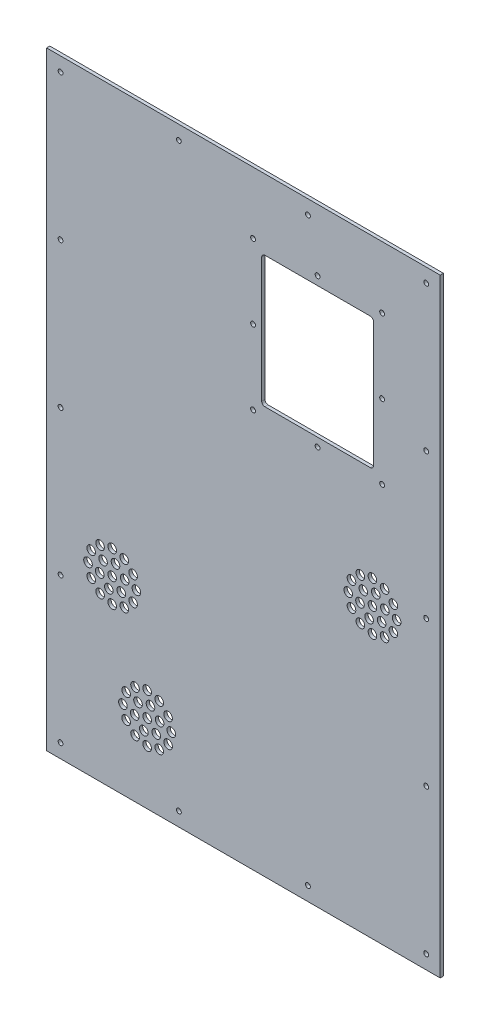
SolidWorks part; units mm, degrees
ref_plane "Спереди" through (0, 0, 0) normal (0, 0, 1) x (1, 0, 0)
ref_plane "Сверху" through (0, 0, 0) normal (0, 1, 0) x (1, 0, 0)
ref_plane "Справа" through (0, 0, 0) normal (1, 0, 0) x (0, 0, -1)
sketch "Эскиз1" plane through (0, 0, 0) normal (0, 0, 1) x (1, 0, 0)
  line L0 (0, 0) -> (366, 0)
  line L1 (0, 0) -> (0, 566)
  line L2 (366, 0) -> (366, 566)
  line L3 (0, 566) -> (366, 566)
  dimension "D1" = 566
  dimension "D2" = 366
extrude "Бобышка-Вытянуть1" add sketch "Эскиз1" along normal blind 3
sketch "Эскиз2" plane through (0, 0, 3) normal (0, 0, 1) x (1, 0, 0)
  line L0 (3, 563) -> (363, 563) construction
  line L1 (3, 563) -> (3, 3) construction
  line L2 (363, 563) -> (363, 3) construction
  line L3 (3, 3) -> (363, 3) construction
  line L4 (0, 566) -> (0, 0) construction
  line L5 (0, 0) -> (366, 0) construction
  dimension "D1" = 560
  dimension "D2" = 360
  dimension "D3" = 3
  dimension "D4" = 3
sketch "Эскиз5" plane through (0, 0, 0) normal (0, 0, -1) x (-1, 0, 0)
  line L0 (-353, 553) -> (-13, 553) construction
  line L1 (-353, 553) -> (-353, 13) construction
  line L2 (-13, 553) -> (-13, 13) construction
  line L3 (-353, 13) -> (-13, 13) construction
  line L4 (-366, 566) -> (0, 566) construction
  line L5 (-366, 0) -> (-366, 566) construction
  line L6 (0, 566) -> (0, 0) construction
  line L7 (0, 0) -> (-366, 0) construction
  line L8 (-366, 23) -> (-343, 23) construction
  line L9 (-366, 23) -> (-366, 0) construction
  line L10 (-343, 23) -> (-343, 0) construction
  line L11 (-366, 0) -> (-343, 0) construction
  line L12 (0, 0) -> (0, 23) construction
  line L13 (0, 0) -> (-23, 0) construction
  line L14 (0, 23) -> (-23, 23) construction
  line L15 (-23, 0) -> (-23, 23) construction
  line L16 (-366, 566) -> (-343, 566) construction
  line L17 (-366, 566) -> (-366, 543) construction
  line L18 (-343, 566) -> (-343, 543) construction
  line L19 (-366, 543) -> (-343, 543) construction
  line L20 (0, 566) -> (0, 543) construction
  line L21 (0, 566) -> (-23, 566) construction
  line L22 (0, 543) -> (-23, 543) construction
  line L23 (-23, 566) -> (-23, 543) construction
  line L24 (-13, 283) -> (-353, 283) construction
  line L25 (-183, 553) -> (-183, 13) construction
  circle A0 centre (-353, 553) radius 2.25
  circle A1 centre (-13, 553) radius 2.25
  circle A3 centre (-243, 553) radius 2.25
  circle A4 centre (-123, 553) radius 2.25
  circle A5 centre (-353, 418) radius 2.25
  circle A6 centre (-353, 283) radius 2.25
  circle A7 centre (-353, 148) radius 2.25
  circle A8 centre (-353, 13) radius 2.25
  circle A11 centre (-13, 418) radius 2.25
  circle A12 centre (-13, 283) radius 2.25
  circle A13 centre (-13, 148) radius 2.25
  circle A14 centre (-13, 13) radius 2.25
  circle A18 centre (-123, 13) radius 2.25
  circle A19 centre (-243, 13) radius 2.25
  dimension "D13" = 4.5
  dimension "D14" = 4.5
  dimension "D15" = 110
  dimension "D17" = 4.5
  dimension "D18" = 4.5
  dimension "D19" = 110
  dimension "D22" = 135
  dimension "D23" = 135
  dimension "D24" = 110
  dimension "D25" = 5
  dimension "D26" = 135
  dimension "D27" = 110
  dimension "D29" = 4.5
  dimension "D31" = 4.5
  dimension "D1" = 13
  dimension "D2" = 13
  dimension "D3" = 13
  dimension "D4" = 13
  dimension "D5" = 23
  dimension "D6" = 23
  dimension "D7" = 23
  dimension "D8" = 23
  dimension "D9" = 23
  dimension "D10" = 23
  dimension "D11" = 23
  dimension "D12" = 23
  dimension "D21" = 5
extrude "Вырез-Вытянуть2" cut sketch "Эскиз5" against normal through all
sketch "Эскиз6" plane through (0, 0, 3) normal (0, 0, 1) x (1, 0, 0)
  line L0 (200, 378.5) -> (200, 500.5) construction
  line L1 (200, 378.5) -> (200, 500.5)
  line L2 (200, 500.5) -> (304, 500.5) construction
  line L3 (200, 500.5) -> (304, 500.5)
  line L4 (304, 500.5) -> (304, 378.5) construction
  line L5 (304, 500.5) -> (304, 378.5)
  line L6 (304, 378.5) -> (200, 378.5) construction
  line L7 (304, 378.5) -> (200, 378.5)
extrude "Вырез-Вытянуть3" cut sketch "Эскиз6" against normal through all
sketch "Эскиз7" plane through (0, 0, 3) normal (0, 0, 1) x (1, 0, 0)
  circle A0 centre (192, 370.5) radius 2.25 construction
  circle A1 centre (192, 370.5) radius 2.25
  circle A2 centre (192, 439.5) radius 2.25 construction
  circle A3 centre (192, 439.5) radius 2.25
  circle A4 centre (192, 508.5) radius 2.25 construction
  circle A5 centre (192, 508.5) radius 2.25
  circle A6 centre (252, 370.5) radius 2.25 construction
  circle A7 centre (252, 370.5) radius 2.25
  circle A8 centre (312, 370.5) radius 2.25 construction
  circle A9 centre (312, 370.5) radius 2.25
  circle A10 centre (252, 508.5) radius 2.25 construction
  circle A11 centre (252, 508.5) radius 2.25
  circle A12 centre (312, 508.5) radius 2.25 construction
  circle A13 centre (312, 508.5) radius 2.25
  circle A14 centre (312, 439.5) radius 2.25 construction
  circle A15 centre (312, 439.5) radius 2.25
  circle A16 centre (312, 370.5) radius 2.25
extrude "Вырез-Вытянуть4" cut sketch "Эскиз7" against normal through all contours A3 | A11 | A13 | A15 | A9 | A7 | A1 | A5
fillet "Fillet2" radius 3 4 edges at (200, 378.5, 1.5) (304, 378.5, 1.5) (304, 500.5, 1.5) (200, 500.5, 1.5)
sketch "Эскиз8" plane through (0, 0, 0) normal (0, 0, -1) x (-1, 0, 0)
  line L0 (-93.5, 73) -> (-93.5, 0) construction
  line L1 (0, 0) -> (-366, 0) construction
  line L2 (-61, 171) -> (0, 171) construction
  line L3 (0, 566) -> (0, 0) construction
  line L4 (-93.5, 73) -> (0, 73) construction
  line L5 (-61, 171) -> (-76.9099, 155.0901) construction
  line L6 (-93.5, 73) -> (-101.9853, 64.5147) construction
  line L7 (-61, 193.5) -> (-61, 148.5) construction
  circle A0 centre (-61, 171) radius 12 construction
  circle A1 centre (-61, 171) radius 22.5 construction
  circle A2 centre (-61, 148.5) radius 4
  circle A3 centre (-69.4853, 162.5147) radius 4
  circle A4 centre (-61, 171) radius 4
  circle A5 centre (-72.25, 151.5144) radius 4
  circle A6 centre (-80.4856, 159.75) radius 4
  circle A7 centre (-83.5, 171) radius 4
  circle A8 centre (-80.4856, 182.25) radius 4
  circle A9 centre (-72.25, 190.4856) radius 4
  circle A10 centre (-61, 193.5) radius 4
  circle A11 centre (-49.75, 190.4856) radius 4
  circle A12 centre (-41.5144, 182.25) radius 4
  circle A13 centre (-38.5, 171) radius 4
  circle A14 centre (-41.5144, 159.75) radius 4
  circle A15 centre (-49.75, 151.5144) radius 4
  circle A16 centre (-72.5911, 174.1058) radius 4
  circle A17 centre (-64.1058, 182.5911) radius 4
  circle A18 centre (-52.5147, 179.4853) radius 4
  circle A19 centre (-49.4089, 167.8942) radius 4
  circle A20 centre (-57.8942, 159.4089) radius 4
  circle A21 centre (-93.5, 73) radius 12 construction
  circle A22 centre (-93.5, 73) radius 22.5 construction
  circle A23 centre (-93.5, 73) radius 4
  circle A24 centre (-93.5, 50.5) radius 4
  circle A25 centre (-101.9853, 64.5147) radius 4
  circle A26 centre (-104.75, 53.5144) radius 4
  circle A27 centre (-112.9856, 61.75) radius 4
  circle A28 centre (-116, 73) radius 4
  circle A29 centre (-112.9856, 84.25) radius 4
  circle A30 centre (-104.75, 92.4856) radius 4
  circle A31 centre (-93.5, 95.5) radius 4
  circle A32 centre (-82.25, 92.4856) radius 4
  circle A33 centre (-74.0144, 84.25) radius 4
  circle A34 centre (-71, 73) radius 4
  circle A35 centre (-74.0144, 61.75) radius 4
  circle A36 centre (-82.25, 53.5144) radius 4
  circle A37 centre (-105.0911, 76.1058) radius 4
  circle A38 centre (-96.6058, 84.5911) radius 4
  circle A39 centre (-85.0147, 81.4853) radius 4
  circle A40 centre (-81.9089, 69.8942) radius 4
  circle A41 centre (-90.3942, 61.4089) radius 4
  point P26 (-61, 171)
  point P52 (-61, 171)
  point P82 (-93.5, 73)
  point P93 (-93.5, 73)
  dimension "D4" = 45
  dimension "D5" = 24
  dimension "D7" = 8
  dimension "D8" = 8
  dimension "D9" = 8
  dimension "D12" = 8
  dimension "D13" = 8
  dimension "D14" = 8
  dimension "D16" = 24
  dimension "D17" = 45
  dimension "D1" = 73
  dimension "D2" = 61
  dimension "D3" = 93.5
  dimension "D6" = 45
  dimension "D15" = 171
  dimension "D20" = 45
  dimension "D10" = 12
  dimension "D11" = 6
  dimension "D18" = 12
  dimension "D19" = 6
extrude "Вырез-Вытянуть5" cut sketch "Эскиз8" against normal through all
sketch "Эскиз9" plane through (0, 0, 0) normal (0, 0, -1) x (-1, 0, 0)
  line L0 (-303, 566) -> (-303, 268) construction
  line L1 (-366, 566) -> (0, 566) construction
  line L2 (-303, 268) -> (-366, 268) construction
  line L3 (-366, 0) -> (-366, 566) construction
  line L4 (-303, 268) -> (-303, 245.5) construction
  line L5 (-303, 268) -> (-311.4853, 259.5147) construction
  circle A0 centre (-303, 268) radius 12 construction
  circle A1 centre (-303, 268) radius 22.5 construction
  circle A2 centre (-303, 268) radius 4
  circle A3 centre (-303, 245.5) radius 4
  circle A4 centre (-311.4853, 259.5147) radius 4
  circle A5 centre (-314.25, 248.5144) radius 4
  circle A6 centre (-322.4856, 256.75) radius 4
  circle A7 centre (-325.5, 268) radius 4
  circle A8 centre (-322.4856, 279.25) radius 4
  circle A9 centre (-314.25, 287.4856) radius 4
  circle A10 centre (-303, 290.5) radius 4
  circle A11 centre (-291.75, 287.4856) radius 4
  circle A12 centre (-283.5144, 279.25) radius 4
  circle A13 centre (-280.5, 268) radius 4
  circle A14 centre (-283.5144, 256.75) radius 4
  circle A15 centre (-291.75, 248.5144) radius 4
  circle A16 centre (-314.5911, 271.1058) radius 4
  circle A17 centre (-306.1058, 279.5911) radius 4
  circle A18 centre (-294.5147, 276.4853) radius 4
  circle A19 centre (-291.4089, 264.8942) radius 4
  circle A20 centre (-299.8942, 256.4089) radius 4
  point P38 (-303, 268)
  point P49 (-303, 268)
  dimension "D3" = 45
  dimension "D4" = 24
  dimension "D5" = 8
  dimension "D1" = 63
  dimension "D2" = 298
  dimension "D6" = 45
  dimension "D7" = 12
  dimension "D8" = 6
extrude "Вырез-Вытянуть6" cut sketch "Эскиз9" against normal through all
